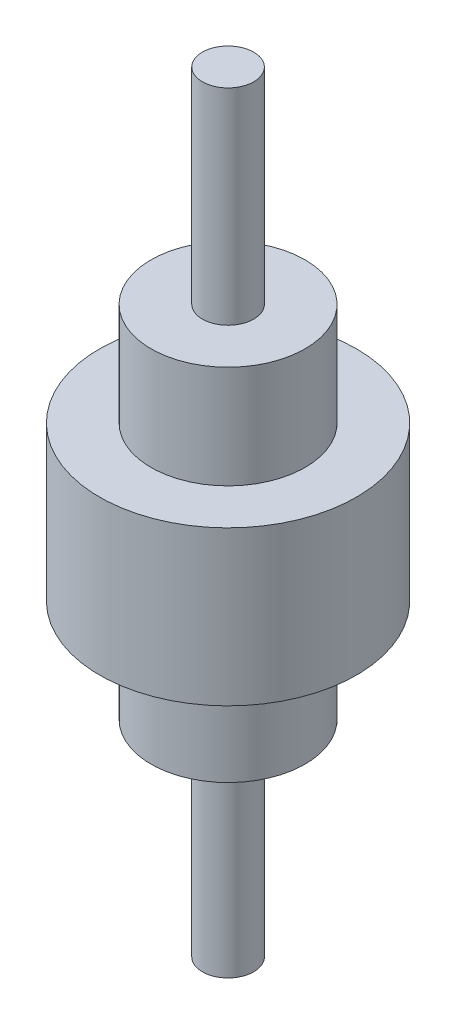
SolidWorks part; units mm, degrees
ref_plane "Front Plane" through (0, 0, 0) normal (0, 0, 1) x (1, 0, 0)
ref_plane "Top Plane" through (0, 0, 0) normal (0, 1, 0) x (1, 0, 0)
ref_plane "Right Plane" through (0, 0, 0) normal (1, 0, 0) x (0, 0, -1)
sketch "Sketch4" plane through (0, 0, 0) normal (0, 0, 1) x (1, 0, 0)
  line L0 (0, 0) -> (0, 3338.0015) construction
  line L1 (0, 0) -> (100, 0)
  line L2 (100, 0) -> (100, 800)
  line L3 (100, 800) -> (300, 800)
  line L4 (300, 800) -> (300, 1200)
  line L5 (300, 1200) -> (500, 1200)
  line L6 (500, 1200) -> (500, 1800)
  line L7 (500, 1800) -> (300, 1800)
  line L8 (300, 1800) -> (300, 2200)
  line L9 (300, 2200) -> (100, 2200)
  line L10 (100, 2200) -> (100, 3000)
  line L11 (100, 3000) -> (0, 3000)
  line L12 (0, 3000) -> (0, 0)
  dimension "D1" = 3000
  dimension "D2" = 800
  dimension "D3" = 400
  dimension "D4" = 100
  dimension "D5" = 300
  dimension "D6" = 500
revolve "Revolve4" add sketch "Sketch4" angle 360 about L0
